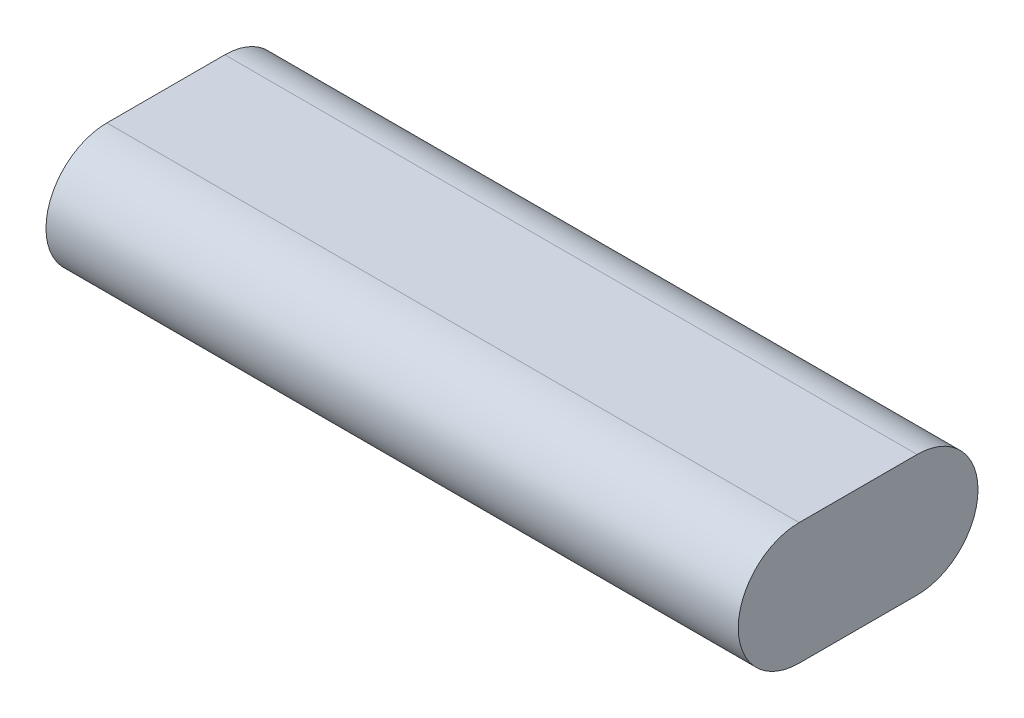
SolidWorks part; units mm, degrees
ref_plane "Front Plane" through (0, 0, 0) normal (0, 0, 1) x (1, 0, 0)
ref_plane "Top Plane" through (0, 0, 0) normal (0, 1, 0) x (1, 0, 0)
ref_plane "Right Plane" through (0, 0, 0) normal (1, 0, 0) x (0, 0, -1)
sketch "Sketch1" plane through (0, 0, 0) normal (1, 0, 0) x (0, 0, -1)
  line L0 (-11.684, 0) -> (11.684, 0) construction
  line L1 (-23.749, -12.065) -> (23.749, -12.065) construction
  line L2 (-23.749, -12.065) -> (-23.749, 12.065) construction
  line L3 (-23.749, 12.065) -> (23.749, 12.065) construction
  line L4 (23.749, -12.065) -> (23.749, 12.065) construction
  line L5 (-23.749, -12.065) -> (23.749, 12.065) construction
  line L6 (-23.749, 12.065) -> (23.749, -12.065) construction
  line L7 (-11.684, 12.065) -> (11.684, 12.065)
  line L8 (-11.684, -12.065) -> (11.684, -12.065)
  arc A0 (-11.684, 12.065) -> (-11.684, -12.065) centre (-11.684, 0) ccw
  arc A1 (11.684, -12.065) -> (11.684, 12.065) centre (11.684, 0) ccw
  point P0 (0, 0)
  point P8 (0, 0)
  dimension "D1" = 47.498
  dimension "D2" = 24.13
extrude "Boss-Extrude1" add sketch "Sketch1" along normal mid plane 137.16
